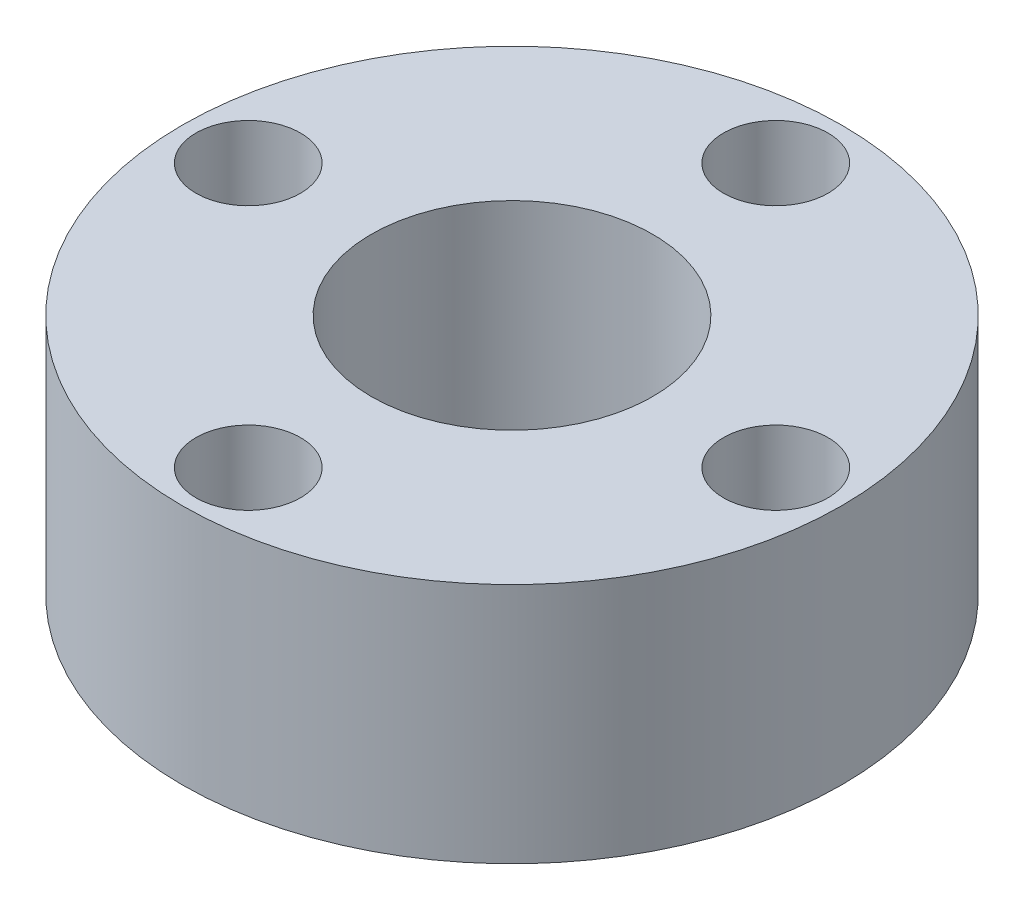
SolidWorks part; units mm, degrees
ref_plane "Front" through (0, 0, 0) normal (0, 0, 1) x (1, 0, 0)
ref_plane "Top" through (0, 0, 0) normal (0, 1, 0) x (1, 0, 0)
ref_plane "Right" through (0, 0, 0) normal (1, 0, 0) x (0, 0, -1)
sketch "Sketch1" plane through (0, 0, 0) normal (0, 1, 0) x (1, 0, 0)
  circle A0 centre (0, 0) radius 9.525
  circle A1 centre (0, 0) radius 7.62 construction
  circle A2 centre (0, 7.62) radius 1.51
  circle A3 centre (7.62, 0) radius 1.51
  circle A4 centre (0, -7.62) radius 1.51
  circle A5 centre (-7.62, 0) radius 1.51
  circle A6 centre (0, 0) radius 4.064
  dimension "D1" = 19.05
  dimension "D2" = 15.24
  dimension "D3" = 3.02
  dimension "D5" = 8.128
  dimension "D4" = 4
extrude "Boss-Extrude1" add sketch "Sketch1" along normal blind 6.985
